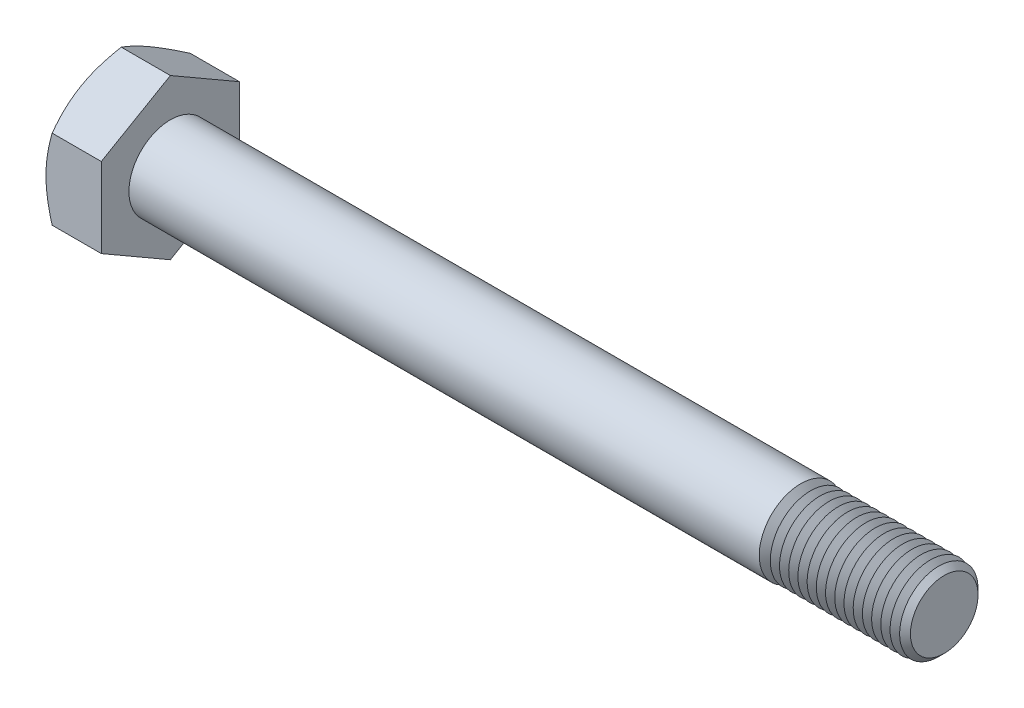
SolidWorks part; units mm, degrees
extrude "BaseHead" add sketch "Sketch1" along normal blind 4
sketch "Sketch1" plane through (0, 0, 0) normal (1, 0, 0) x (0, 0, -1)
  line L0 (5, 2.8868) -> (5, -2.8868)
  line L1 (-5, 2.8868) -> (-5, -2.8868)
  line L2 (5, -2.8868) -> (0, -5.7735)
  line L3 (0, -5.7735) -> (-5, -2.8868)
  line L4 (5, 2.8868) -> (0, 5.7735)
  line L5 (0, 5.7735) -> (-5, 2.8868)
  dimension "Width_flats" = 10
  dimension "D2" = 120
  dimension "D3" = 5
  dimension "D4" = 5
  dimension "D5" = 5
ref_plane "Plane1" through (0, 0, 0) normal (0, 0, 1) x (1, 0, 0)
ref_plane "Plane2" through (0, 0, 0) normal (0, 1, 0) x (1, 0, 0)
ref_plane "Plane3" through (0, 0, 0) normal (1, 0, 0) x (0, 0, -1)
sketch "BodySke" plane through (0, 0, 0) normal (0, 0, 1) x (1, 0, 0)
  line L1 (0, 0) -> (60, 0)
  line L2 (0, 0) -> (0, 3)
  line L4 (60, 0) -> (60, 2.4455)
  line L5 (4, 5.7735) -> (4, 2.8868) construction
  line L6 (60, 2.4455) -> (59.4455, 3)
  line L7 (0, 0) -> (110.49, 0) construction
  line L8 (60, -2.4455) -> (59.4455, -3) construction
  line L9 (0, 2.8868) -> (0, -2.8868) construction
  line L10 (5, 15.24) -> (5, -1.27) construction
  line L11 (50, 15.24) -> (50, -1.27) construction
  line L12 (4, 2.8868) -> (4, -2.8868) construction
  line L15 (0, 3) -> (59.4455, 3)
  dimension "Body_ch_ang" = 45
  dimension "Minor_dia" = 4.891
  dimension "Diameter" = 6
revolve "BaseBody" add sketch "BodySke" angle 360 about L7
cosmetic thread "ThreadCosmetic" [suppressed] parameters "Thread_length"=10, "Thread_minor"=4.891
fillet "HeadFillet" [suppressed] radius 0.25
sketch "Sketch3" plane through (0, 0, 0) normal (0, 0, 1) x (1, 0, 0)
  line L0 (0, 5) -> (3.3333, 10.7735)
  line L1 (0, 5.7735) -> (0, 2.8868) construction
  line L2 (3.3333, 10.7735) -> (3.3333, 15.7735)
  line L3 (3.3333, 15.7735) -> (-10, 15.7735)
  line L4 (-10, 15.7735) -> (-10, 5)
  line L5 (-10, 5) -> (0, 5)
  line L6 (0, 0) -> (99.06, 0) construction
  line L7 (4, 5.7735) -> (0, 5.7735) construction
  dimension "D4" = 5
  dimension "D1" = 5
  dimension "D2" = 5
  dimension "D3" = 10
  dimension "Head_ch_ang" = 30
revolve "HeadChamfer" cut sketch "Sketch3" angle 360 about L6
sketch "ThdSchSke" plane through (0, 0, 0) normal (0, 0, 1) x (1, 0, 0)
  line L0 (50, -2.4455) -> (49.6117, -3)
  line L1 (50, -2.4455) -> (50.3883, -3)
  line L2 (50.3883, -3) -> (50.3883, -3.75)
  line L3 (-3.175, 0) -> (5.1513, 0) construction
  line L5 (50.3883, -3.75) -> (49.6117, -3.75)
  line L6 (49.6117, -3.75) -> (49.6117, -3)
  dimension "Thread_minor" = 4.891
  dimension "Diameter" = 6
  dimension "Start" = 50
revolve "ThreadSchematic" cut sketch "ThdSchSke" angle 360 about L3
pattern_linear "ThdSchPat" count 15 spacing 0.6667 along (1, 0, 0) of "ThreadSchematic"
equation "\"D3@Sketch1\" = \"Width_flats@Sketch1\" / 2"
equation "\"D4@Sketch1\" = \"D3@Sketch1\""
equation "\"D5@Sketch1\" = \"D4@Sketch1\""
equation "\"Thread_minor@ThreadCosmetic\" = \"Minor_dia@BodySke\""
equation "\"D1@Sketch3\" = \"Width_flats@Sketch1\" / 2"
equation "\"Thread_length@ThreadCosmetic\" = ((sgn( (\"Length@BodySke\" - \"Advance@BodySke\" ) - \"Thread_nom@BodySke\" )-1)*( (\"Length@BodySke\" - \"Advance@BodySke\" ) - \"Thread_nom@BodySke\" ))/-2+ \"Thread_nom@BodySke\""
equation "\"Thread_minor@ThdSchSke\" = \"Minor_dia@BodySke\""
equation "\"Diameter@ThdSchSke\" = \"Diameter@BodySke\""
equation "\"Overcut@ThdSchSke\" = \"Diameter@BodySke\" * 1.25"
equation "\"Start@ThdSchSke\" = \"Head_ht@BaseHead\" + \"Length@BodySke\" - \"Thread_length@ThreadCosmetic\"  '---Non-countersunk---"
equation "\"Num_threads@ThdSchPat\" = int( \"Thread_length@ThreadCosmetic\" / \"Advance@BodySke\" + 0.999 )  + 1"
equation "\"Advance@ThdSchPat\" = \"Thread_length@ThreadCosmetic\" /  (\"Num_threads@ThdSchPat\" - 1) 'relax it"
equation "\"Num_threads@ThdSchPat\" = \"Num_threads@ThdSchPat\" - sgn( \"Num_threads@ThdSchPat\" - 1) '---chamfered tips only---"
